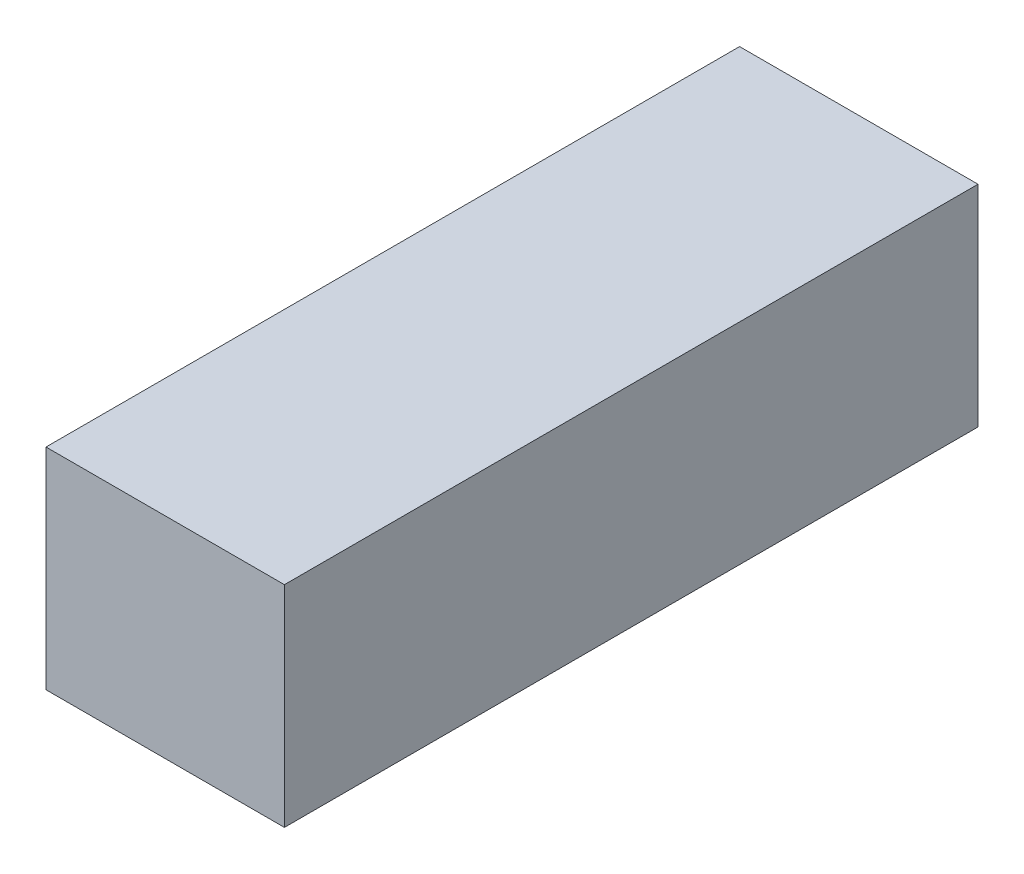
SolidWorks part; units mm, degrees
ref_plane "正面" through (0, 0, 0) normal (1, 0, 0) x (0, 1, 0)
ref_plane "平面" through (0, 0, 0) normal (0, 0, 1) x (0, 1, 0)
ref_plane "右側面" through (0, 0, 0) normal (0, 1, 0) x (-1, 0, 0)
sketch "ｽｹｯﾁ1" plane through (0, 0, 0) normal (0, 0, 1) x (0, 1, 0)
  line L1 (0, 0) -> (48.5, 0)
  line L2 (0, 0) -> (0, 55)
  line L3 (0, 55) -> (48.5, 55)
  line L4 (48.5, 0) -> (48.5, 55)
  line L5 (0, 0) -> (48.5, 55) construction
  line L6 (0, 55) -> (48.5, 0) construction
  point P4 (24.25, 27.5)
  dimension "D1" = 48.5
  dimension "D2" = 55
extrude "ﾎﾞｽ - 押し出し1" add sketch "ｽｹｯﾁ1" along normal blind 160
